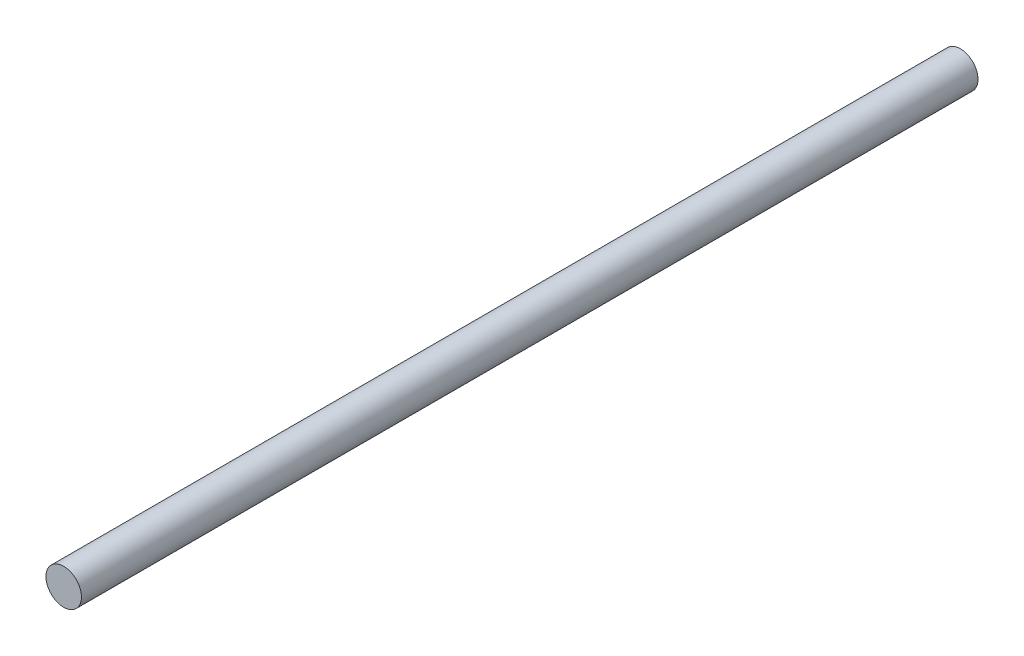
SolidWorks part; units mm, degrees
ref_plane "Front Plane" through (0, 0, 0) normal (0, 0, 1) x (1, 0, 0)
ref_plane "Top Plane" through (0, 0, 0) normal (0, 1, 0) x (1, 0, 0)
ref_plane "Right Plane" through (0, 0, 0) normal (1, 0, 0) x (0, 0, -1)
sketch "Sketch1" plane through (0, 0, 0) normal (0, 0, 1) x (1, 0, 0)
  circle A0 centre (0, 0) radius 2.375
  dimension "D1" = 4.75
extrude "Boss-Extrude1" add sketch "Sketch1" along normal blind 120
